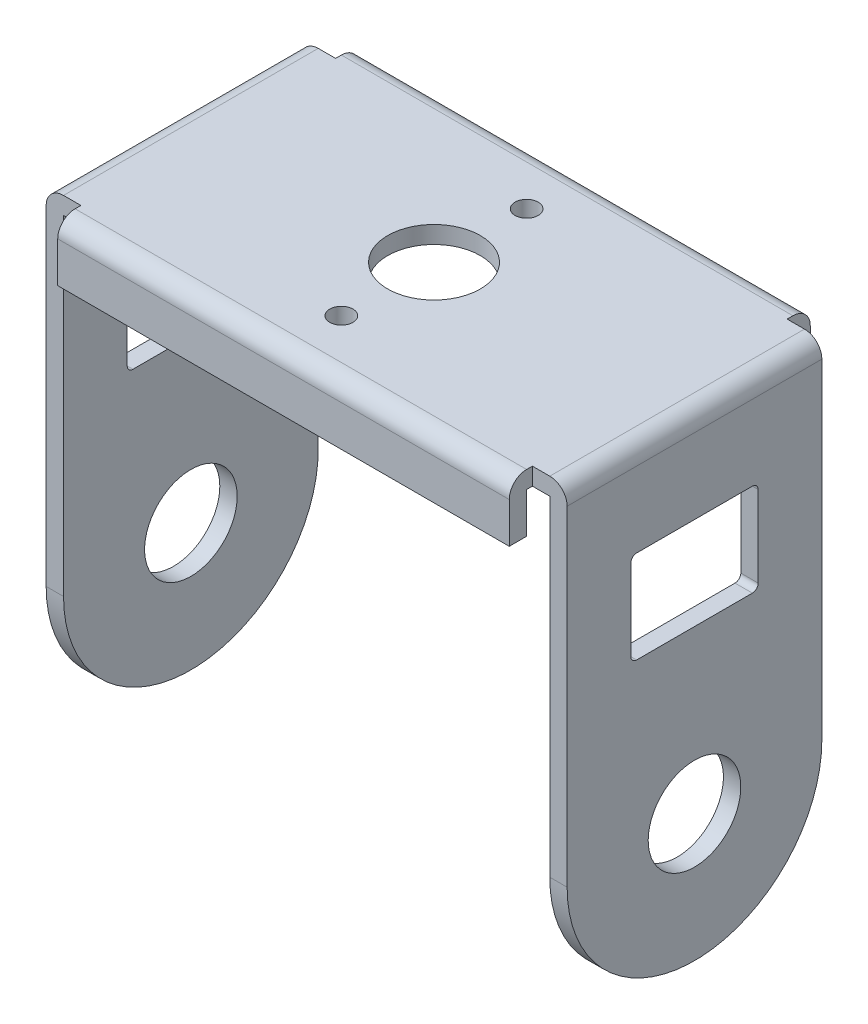
SolidWorks part; units mm, degrees
ref_plane "Front Plane" through (0, 0, 0) normal (0, 0, 1) x (1, 0, 0)
ref_plane "Top Plane" through (0, 0, 0) normal (0, 1, 0) x (1, 0, 0)
ref_plane "Right Plane" through (0, 0, 0) normal (1, 0, 0) x (0, 0, -1)
ref_plane "Plane1" through (22.5, 0, 0) normal (1, 0, 0) x (0, 0, -1)
sketch "Sketch1" plane through (22.5, 0, 0) normal (1, 0, 0) x (0, 0, -1)
  line L0 (-11, 30) -> (-11, 0)
  line L1 (11, 0) -> (11, 30)
  line L2 (11, 30) -> (-11, 30)
  arc A0 (-11, 0) -> (11, 0) centre (0, 0) ccw
extrude "Boss-Extrude1" add sketch "Sketch1" against normal blind 45
sketch "Sketch2" plane through (0, 0, 11) normal (0, 0, 1) x (1, 0, 0)
  line L0 (-21, -17.7124) -> (21, -17.7124)
  line L1 (21, -17.7124) -> (21, 28.5)
  line L2 (21, 28.5) -> (-21, 28.5)
  line L3 (-21, 28.5) -> (-21, -17.7124)
extrude "Cut-Extrude1" cut sketch "Sketch2" against normal through all
sketch "Sketch3" plane through (0, 0, -11) normal (0, 0, -1) x (-1, 0, 0)
  line L0 (19.5, 28.5) -> (-19.5, 28.5)
  line L1 (-19.5, 28.5) -> (-19.5, 30)
  line L2 (-19.5, 30) -> (19.5, 30)
  line L3 (19.5, 30) -> (19.5, 28.5)
extrude "Boss-Extrude2" add sketch "Sketch3" along normal blind 2
sketch "Sketch4" plane through (0, 28.5, 0) normal (0, -1, 0) x (1, 0, 0)
  line L0 (-19.5, -11.5) -> (19.5, -11.5)
  line L1 (19.5, -11.5) -> (19.5, -13)
  line L2 (19.5, -13) -> (-19.5, -13)
  line L3 (-19.5, -13) -> (-19.5, -11.5)
extrude "Boss-Extrude3" add sketch "Sketch4" along normal blind 3.5
sketch "Sketch5" plane through (0, 0, 11) normal (0, 0, 1) x (1, 0, 0)
  line L0 (19.5, 28.5) -> (-19.5, 28.5)
  line L1 (-19.5, 28.5) -> (-19.5, 30)
  line L2 (-19.5, 30) -> (19.5, 30)
  line L3 (19.5, 30) -> (19.5, 28.5)
extrude "Boss-Extrude4" add sketch "Sketch5" along normal blind 2
sketch "Sketch6" plane through (0, 28.5, 0) normal (0, -1, 0) x (1, 0, 0)
  line L0 (19.5, 11.5) -> (-19.5, 11.5)
  line L1 (-19.5, 11.5) -> (-19.5, 13)
  line L2 (-19.5, 13) -> (19.5, 13)
  line L3 (19.5, 13) -> (19.5, 11.5)
extrude "Boss-Extrude5" add sketch "Sketch6" along normal blind 3.5
hole_wizard "Ø8.0 (8) Diameter Hole1" positions "Sketch8" profile "Sketch7" hole size "Ø8.0" standard "ANSI Metric"
sketch "Sketch8" plane through (0, 28.5, 0) normal (0, -1, 0) x (-1, 0, 0)
  point P0 (0, 0)
sketch "Sketch7" plane through (0, 28.5, 0) normal (1, 0, 0) x (0, 0, -1)
  line L0 (0, 0) -> (0, 1.5)
  line L1 (0, 1.5) -> (4, 1.5)
  line L2 (4, 1.5) -> (4, 0)
  line L5 (4, 0) -> (0, 0)
  line L11 (0, -6.35) -> (0, 107.95) construction
  dimension "Thru Hole Dia." = 8
  dimension "Thru Hole Depth" = 1.5
hole_wizard "Ø8.0 (8) Diameter Hole2" positions "Sketch10" profile "Sketch9" hole size "Ø8.0" standard "ANSI Metric"
sketch "Sketch10" plane through (-21, 0, 0) normal (1, 0, 0) x (0, 0, -1)
  point P0 (0, 0)
sketch "Sketch9" plane through (-21, 0, 0) normal (0, 1, 0) x (0, 0, -1)
  line L0 (0, 0) -> (0, 1.5)
  line L1 (0, 1.5) -> (4, 1.5)
  line L2 (4, 1.5) -> (4, 0)
  line L5 (4, 0) -> (0, 0)
  line L11 (0, -6.35) -> (0, 107.95) construction
  dimension "Thru Hole Dia." = 8
  dimension "Thru Hole Depth" = 1.5
hole_wizard "Ø8.0 (8) Diameter Hole3" positions "Sketch12" profile "Sketch11" hole size "Ø8.0" standard "ANSI Metric"
sketch "Sketch12" plane through (21, 0, 0) normal (-1, 0, 0) x (0, 0, 1)
  point P0 (0, 0)
sketch "Sketch11" plane through (21, 0, 0) normal (0, 1, 0) x (0, 0, 1)
  line L0 (0, 0) -> (0, 1.5)
  line L1 (0, 1.5) -> (4, 1.5)
  line L2 (4, 1.5) -> (4, 0)
  line L5 (4, 0) -> (0, 0)
  line L11 (0, -6.35) -> (0, 107.95) construction
  dimension "Thru Hole Dia." = 8
  dimension "Thru Hole Depth" = 1.5
fillet "Fillet1" radius 1.5 4 edges at (-22.5, 30, 0) (0, 30, 13) (0, 30, -13) (22.5, 30, 0)
sketch "Sketch13" plane through (0, 30, 0) normal (0, 1, 0) x (1, 0, 0)
  line L0 (0, 8) -> (0, -8) construction
  circle A0 centre (0, 8) radius 1
  circle A1 centre (0, -8) radius 1
  point P3 (0, 0)
  dimension "D2" = 2
  dimension "D1" = 16
extrude "Cut-Extrude2" cut sketch "Sketch13" against normal blind 2
sketch "Sketch14" plane through (22.5, 0, 0) normal (1, 0, 0) x (0, 0, -1)
  line L0 (0, 28.5) -> (0, -11) construction
  line L1 (11, 28.5) -> (-11, 28.5) construction
  line L2 (5.5, 22) -> (-5.5, 22)
  line L3 (-5.5, 22) -> (-5.5, 14)
  line L4 (-5.5, 14) -> (5.5, 14)
  line L5 (5.5, 22) -> (5.5, 14)
  arc A0 (-11, 0) -> (11, 0) centre (0, 0) ccw construction
  point P12 (0, 14)
  point P13 (0, 22)
  dimension "D1" = 8
  dimension "D2" = 5.5
  dimension "D3" = 6.5
extrude "Cut-Extrude3" cut sketch "Sketch14" against normal blind 45
fillet "Fillet2" radius 0.5 8 edges at (-21.75, 14, 5.5) (21.75, 14, -5.5) (-21.75, 14, -5.5) (21.75, 22, -5.5) (-21.75, 22, -5.5) (21.75, 22, 5.5) (-21.75, 22, 5.5) (21.75, 14, 5.5)
